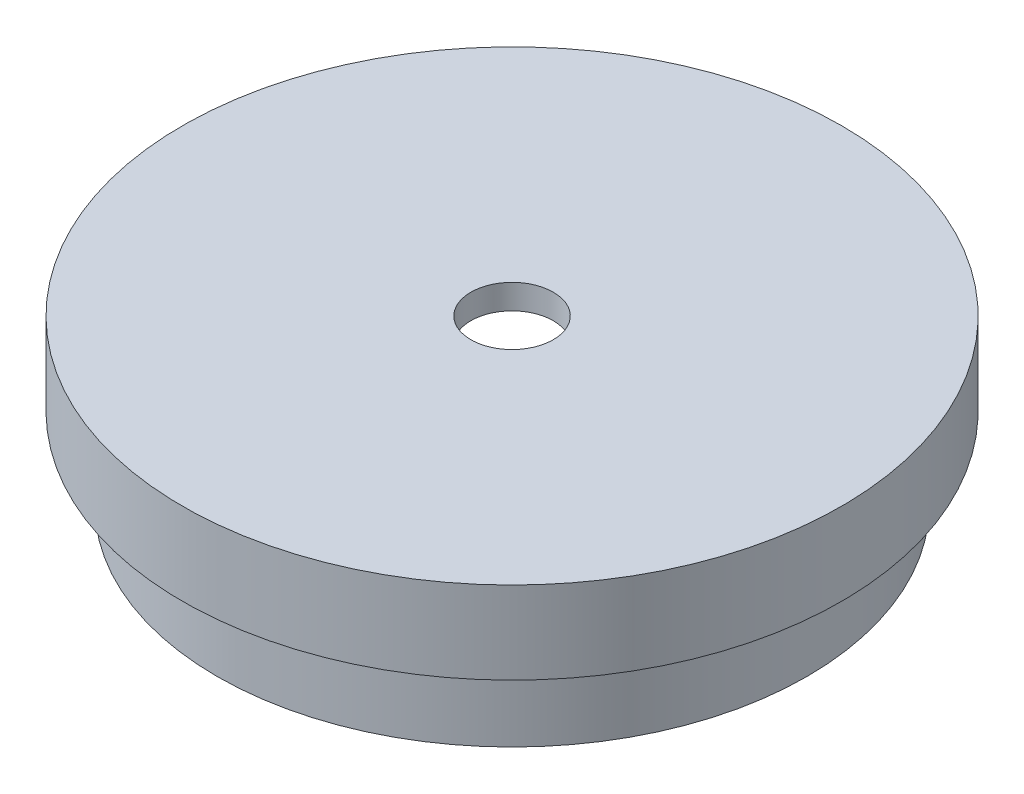
SolidWorks part; units mm, degrees
ref_plane "Front Plane" through (0, 0, 0) normal (0, 0, 1) x (1, 0, 0)
ref_plane "Top Plane" through (0, 0, 0) normal (0, 1, 0) x (1, 0, 0)
ref_plane "Right Plane" through (0, 0, 0) normal (1, 0, 0) x (0, 0, -1)
sketch "Sketch1" plane through (0, 0, 0) normal (0, 0, 1) x (1, 0, 0)
  line L0 (17.9, 0) -> (17.9, 5)
  line L1 (17.9, 5) -> (20, 5)
  line L2 (20, 5) -> (20, 10)
  line L3 (20, 10) -> (2.5, 10)
  line L4 (2.5, 10) -> (2.5, 8.5)
  line L5 (2.5, 8.5) -> (16.4, 8.5)
  line L6 (16.4, 8.5) -> (16.4, 0)
  line L7 (16.4, 0) -> (17.9, 0)
  line L8 (0, 0) -> (0, 10) construction
  line L9 (0, 10) -> (2.5, 10) construction
  point P12 (17.15, 0)
  dimension "D1" = 2.5
  dimension "D2" = 20
  dimension "D3" = 1.5
  dimension "D4" = 2.1
  dimension "D5" = 10
  dimension "D6" = 5
  dimension "D7" = 1.5
revolve "Revolve1" add sketch "Sketch1" angle 360 about L8
